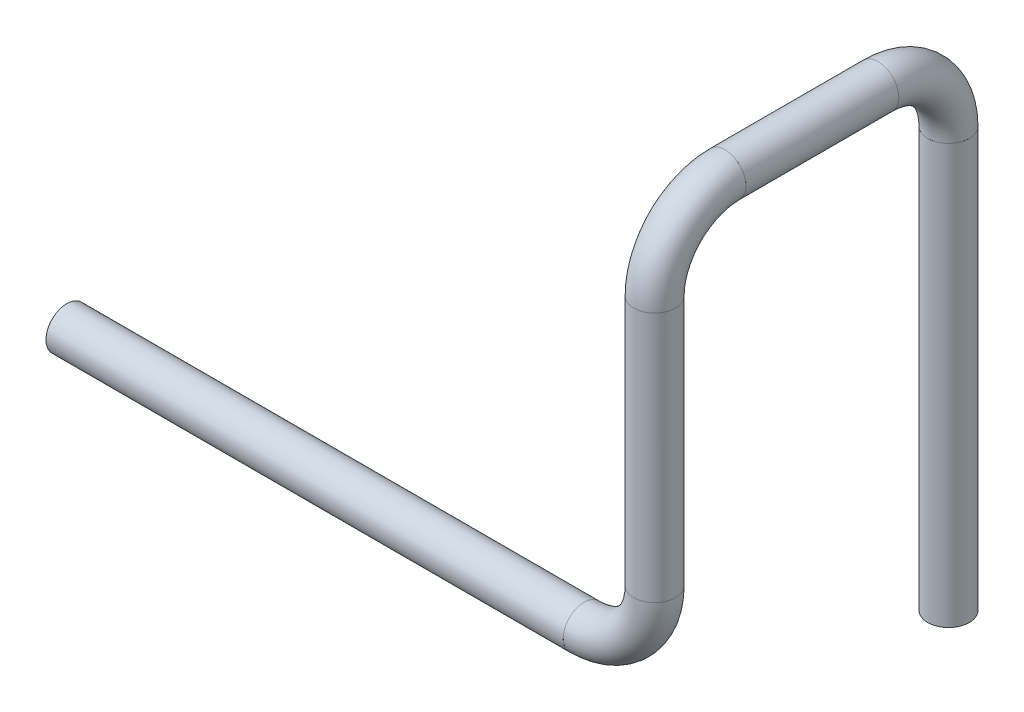
SolidWorks part; units mm, degrees
ref_plane "Ebene vorne" through (0, 0, 0) normal (0, 0, 1) x (1, 0, 0)
ref_plane "Ebene oben" through (0, 0, 0) normal (0, 1, 0) x (1, 0, 0)
ref_plane "Ebene rechts" through (0, 0, 0) normal (1, 0, 0) x (0, 0, -1)
sketch3d "3D-Skizze1"
  line L0 (0, 0, 0) -> (264, 0, 0)
  line L1 (300, 36, 0) -> (300, 164, 0)
  line L2 (300, 200, -36) -> (300, 200, -114)
  line L3 (300, 164, -150) -> (300, -50, -150)
  arc A0 (300, 164, 0) -> (300, 200, -36) centre (300, 164, -36) ccw
  arc A1 (264, 0, 0) -> (300, 36, 0) centre (264, 36, 0) ccw
  arc A2 (300, 200, -114) -> (300, 164, -150) centre (300, 164, -114) ccw
  point P7 (300, 200, 0)
  point P8 (264, 164, -36)
  point P11 (300, 0, 0)
  point P12 (264, 36, 36)
  point P16 (300, 200, -150)
  point P17 (264, 164, -114)
other "Rohr 21.3 X 2.3(1)"
ref_plane "Ebene1" through (0, 0, 0) normal (1, 0, 0) x (0, 0, -1)
sketch "Sketch1" plane through (0, 0, 0) normal (1, 0, 0) x (0, 0, -1)
  circle A0 centre (0, 0) radius 8.35
  circle A1 centre (0, 0) radius 10.65
  point P3 (0, 0)
  dimension "In_dia" = 16.7
  dimension "Out_dia" = 21.3
equation "\"Länge\"= \"D1@3D-Skizze1\" + \"D2@3D-Skizze1\" + \"D3@3D-Skizze1\" + ( 2 * \"D4@3D-Skizze1\" )"
